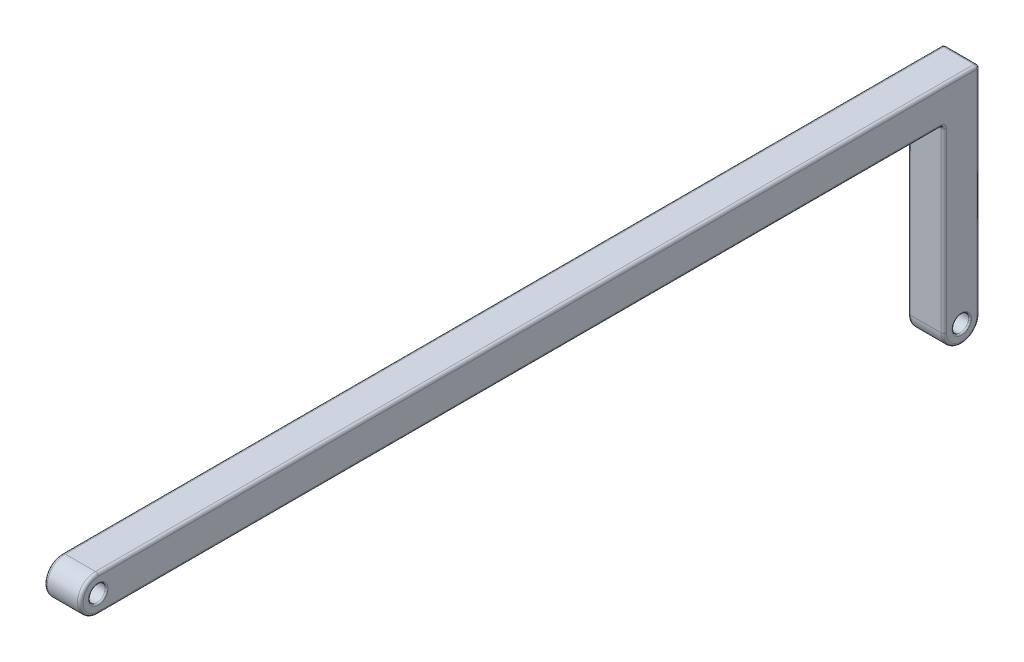
SolidWorks part; units mm, degrees
ref_plane "Front Plane" through (0, 0, 0) normal (0, 0, 1) x (1, 0, 0)
ref_plane "Top Plane" through (0, 0, 0) normal (0, 1, 0) x (1, 0, 0)
ref_plane "Right Plane" through (0, 0, 0) normal (1, 0, 0) x (0, 0, -1)
sketch "Sketch1" plane through (0, 0, 0) normal (1, 0, 0) x (0, 0, -1)
  line L1 (0, 0) -> (60, 0)
  line L8 (0, 0) -> (0, -2.5) construction
  line L12 (60, 0) -> (60, -2.5) construction
  line L13 (0, -2.5) -> (58.75, -2.5)
  line L16 (60, -1.25) -> (61.25, -1.25) construction
  line L17 (60, 0) -> (61.25, 0)
  line L18 (61.25, 0) -> (61.25, -15)
  line L19 (61.25, -15) -> (58.75, -15) construction
  line L20 (58.75, -15) -> (58.75, -2.5)
  circle A0 centre (0, -1.25) radius 0.575
  arc A1 (0, -2.5) -> (0, 0) centre (0, -1.25) cw
  arc A4 (58.75, -15) -> (61.25, -15) centre (60, -15) ccw
  circle A5 centre (60, -15) radius 0.575
  dimension "D1" = 1.15
  dimension "D4" = 1.25
  dimension "D3" = 60
  dimension "D7" = 1.15
  dimension "D2" = 2.5
  dimension "D5" = 15
  dimension "D6" = 2.5
extrude "Boss-Extrude1" add sketch "Sketch1" along normal blind 2.5
fillet "Fillet2" radius 0.1 4 edges at (0, -1.25, -0.575) (2.5, -1.25, -0.575) (0, -15, -60.575) (2.5, -15, -60.575)
fillet "Fillet3" radius 0.2 14 edges at (2.5, -2.5, -29.375) (2.5, -1.25, 1.25) (0, -2.5, -29.375) (0, -1.25, 1.25) (2.5, -7.5, -61.25) (2.5, -16.25, -60) (0, -7.5, -61.25) (0, -16.25, -60) (1.25, 0, -61.25) (2.5, 0, -30.625) (0, 0, -30.625) (1.25, -2.5, -58.75) (2.5, -8.75, -58.75) (0, -8.75, -58.75)
